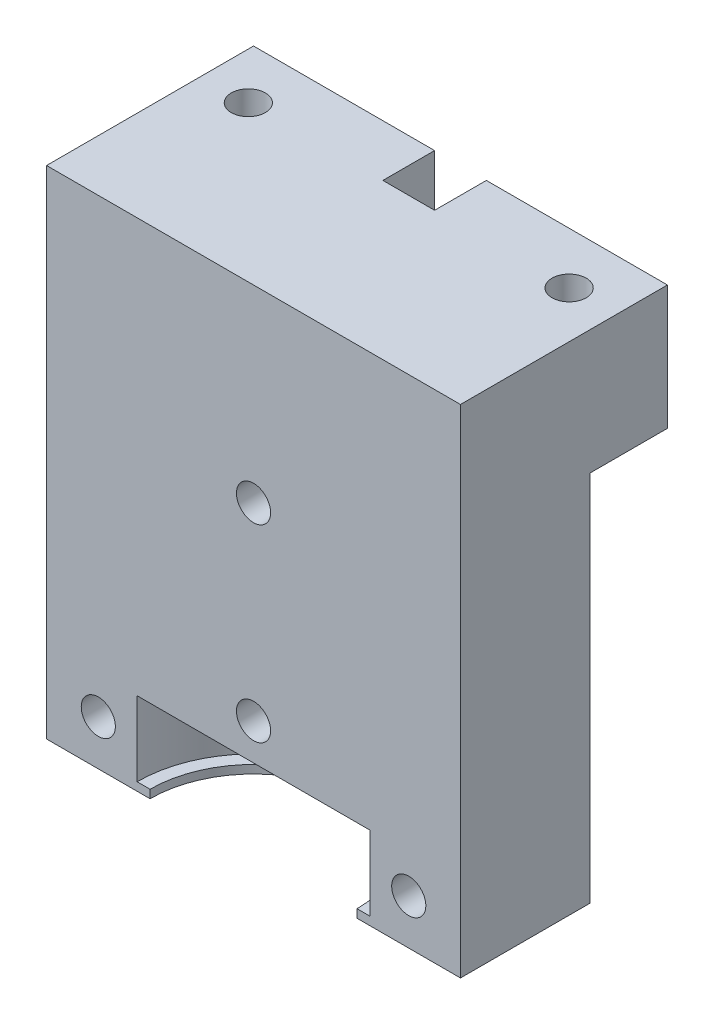
SolidWorks part; units mm, degrees
ref_plane "Front Plane" through (0, 0, 0) normal (0, 0, 1) x (1, 0, 0)
ref_plane "Top Plane" through (0, 0, 0) normal (0, 1, 0) x (1, 0, 0)
ref_plane "Right Plane" through (0, 0, 0) normal (1, 0, 0) x (0, 0, -1)
sketch "Sketch1" plane through (0, 0, 0) normal (0, 1, 0) x (1, 0, 0)
  line L1 (20, 20) -> (-20, 20)
  line L2 (20, 20) -> (20, -20)
  line L3 (20, -20) -> (-20, -20)
  line L4 (-20, 20) -> (-20, -20)
  line L5 (0, -20) -> (0, 20) construction
  line L6 (20, 0) -> (-20, 0) construction
  point P0 (0, 0)
extrude "Boss-Extrude1" add sketch "Sketch1" against normal blind 48
hole_wizard "M4x0.7 Tapped Hole1" positions "Sketch2" profile "Sketch3" tap size "M4x0.7" standard "ANSI Metric" end condition through all
sketch "Sketch2" plane through (0, 0, 0) normal (0, 1, 0) x (1, 0, 0)
  line L1 (-15.5, -15) -> (15.5, -15)
  line L2 (-15.5, -15) -> (-15.5, 15)
  line L3 (-15.5, 15) -> (15.5, 15)
  line L4 (15.5, -15) -> (15.5, 15)
  line L5 (15.5, 0) -> (0, 0) construction
  line L6 (0, 0) -> (0, -15) construction
  point P2 (-15.5, 15)
  point P4 (15.5, 15)
  point P6 (15.5, -15)
  point P8 (-15.5, -15)
  point P130 (-15.5, 15.5)
  point P131 (15.5, -15.5)
  point P132 (0, 0)
  dimension "D1" = 31
  dimension "D2" = 30
sketch "Sketch3" plane through (-15.5, 0, -15) normal (1, 0, 0) x (0, 0, 1)
  line L0 (0, 0) -> (0, 48)
  line L1 (0, 48) -> (1.65, 48)
  line L2 (1.65, 48) -> (1.65, 0)
  line L5 (1.65, 0) -> (0, 0)
  line L11 (0, -6.35) -> (0, 107.95) construction
  dimension "Thread Major Dia." = 3.3
  dimension "Thru Tap Drill Depth" = 48
sketch "Sketch10" plane through (0, 0, 0) normal (0, 1, 0) x (1, 0, 0)
  line L0 (20, -20) -> (20, 20) construction
  line L1 (-20, -20) -> (20, -20)
  line L2 (-20, -20) -> (-20, 0)
  line L3 (-20, 0) -> (20, 0)
  line L4 (20, -20) -> (20, 0)
extrude "Cut-Extrude4" cut sketch "Sketch10" against normal through all
sketch "Sketch11" plane through (0, 0, 0) normal (0, 0, 1) x (1, 0, 0)
  line L0 (0, 0) -> (0, -40) construction
  line L1 (0, -40) -> (11.25, -40)
  line L2 (0, -40) -> (0, -47.2)
  line L3 (0, -47.2) -> (11.25, -47.2)
  line L4 (11.25, -40) -> (11.25, -47.2)
  line L5 (20, 0) -> (-20, 0) construction
  dimension "D1" = 40
  dimension "D2" = 7.2
  dimension "D3" = 22.5
revolve "Cut-Revolve2" cut sketch "Sketch11" angle 360 about L0
sketch "Sketch12" plane through (0, -48, 0) normal (0, -1, 0) x (1, 0, 0)
  line L0 (20, 0) -> (-20, 0) construction
  circle A0 centre (0, 0) radius 10
  dimension "D1" = 20
extrude "Cut-Extrude5" cut sketch "Sketch12" against normal up to next
hole_wizard "M4x0.7 Tapped Hole2" positions "Sketch13" profile "Sketch14" tap size "M4x0.7" standard "ANSI Metric" end condition through all
sketch "Sketch13" plane through (0, 0, -20) normal (0, 0, -1) x (-1, 0, 0)
  line L0 (-15, -43.6281) -> (15, -43.6281) construction
  line L3 (0, -43.6281) -> (0, -36.4844) construction
  line L4 (0, -36.4844) -> (0, -18.2422) construction
  line L5 (0, -18.2422) -> (0, 0) construction
  line L8 (10, -47.2) -> (-10, -47.2) construction
  point P8 (15, -43.6281)
  point P10 (-15, -43.6281)
  point P12 (0, -36.4844)
  point P14 (0, -18.2422)
  point P33 (0, 0)
  dimension "D1" = 30
  dimension "D2" = 3.5719
  dimension "D3" = 7.1437
sketch "Sketch14" plane through (-15, -43.6281, -20) normal (1, 0, 0) x (0, 1, 0)
  line L0 (0, 0) -> (0, 20)
  line L1 (0, 20) -> (1.65, 20)
  line L2 (1.65, 20) -> (1.65, 0)
  line L5 (1.65, 0) -> (0, 0)
  line L11 (0, -6.35) -> (0, 107.95) construction
  dimension "Thru Tap Drill Dia." = 3.3
  dimension "Thru Tap Drill Depth" = 20
cosmetic thread "Hole Thread1" parameters "D2"=4
cosmetic thread "Hole Thread2" parameters "D2"=4
cosmetic thread "Hole Thread3" parameters "D2"=4
cosmetic thread "Hole Thread4" parameters "D2"=4
sketch "Sketch15" plane through (0, -48, 0) normal (0, -1, 0) x (1, 0, 0)
  line L1 (-20, -12.5) -> (20, -12.5)
  line L2 (-20, -12.5) -> (-20, -20)
  line L3 (-20, -20) -> (20, -20)
  line L4 (20, -12.5) -> (20, -20)
  line L5 (-20, -20) -> (-20, 0) construction
  point P4 (-20, -12.6534)
  point P7 (0, 0)
  dimension "D1" = 7.5
extrude "Cut-Extrude6" cut sketch "Sketch15" against normal blind 36
sketch "Sketch16" plane through (0, -12, 0) normal (0, -1, 0) x (1, 0, 0)
  line L0 (-20, -20) -> (20, -20) construction
  line L1 (-2.5, -20) -> (2.5, -20)
  line L2 (-2.5, -20) -> (-2.5, -15)
  line L3 (-2.5, -15) -> (2.5, -15)
  line L4 (2.5, -20) -> (2.5, -15)
  line L5 (0, -15) -> (0, 0) construction
  dimension "D1" = 5
  dimension "D2" = 5
extrude "Cut-Extrude7" cut sketch "Sketch16" against normal through all
